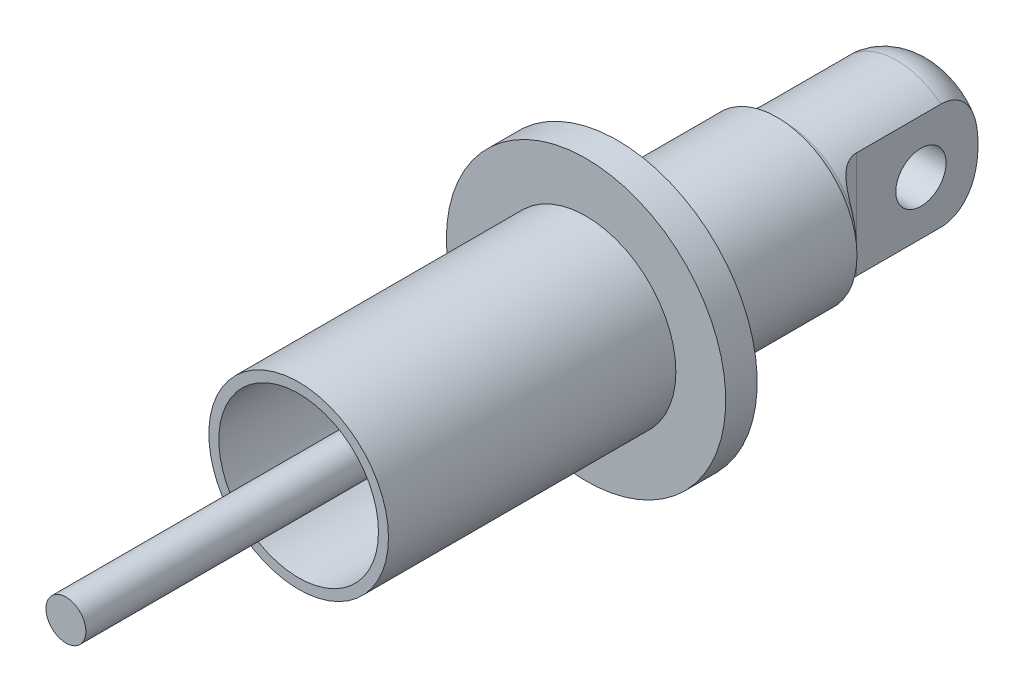
SolidWorks part; units mm, degrees
ref_plane "Front Plane" through (0, 0, 0) normal (0, 0, 1) x (1, 0, 0)
ref_plane "Top Plane" through (0, 0, 0) normal (0, 1, 0) x (1, 0, 0)
ref_plane "Right Plane" through (0, 0, 0) normal (1, 0, 0) x (0, 0, -1)
sketch "Sketch1" plane through (0, 0, 0) normal (0, 0, 1) x (1, 0, 0)
  circle A0 centre (0, 0) radius 12.7
extrude "Boss-Extrude1" add sketch "Sketch1" along normal blind 25.4
ref_plane "Plane1" through (0, 0, 0) normal (0, 1, 0) x (1, 0, 0)
sketch "Sketch3" plane through (0, 0, 0) normal (0, 1, 0) x (1, 0, 0)
  line L0 (12.7, 0) -> (-12.7, 0) construction
  line L2 (0, 0) -> (0, 25.4) construction
  line L3 (0, 25.4) -> (4.65, 25.4)
  line L4 (11, 19.05) -> (11, 1.5875)
  line L5 (12.5875, 0) -> (12.7, 0)
  line L6 (12.5875, 0) -> (0, 0)
  line L7 (0, 0) -> (0, 25.4)
  arc A0 (11, 19.05) -> (4.65, 25.4) centre (4.65, 19.05) ccw
  arc A1 (12.5875, 0) -> (11, 1.5875) centre (12.5875, 1.5875) cw
  point P4 (0, 0)
  point P14 (11, 0)
  dimension "D1" = 6.35
  dimension "D2" = 1.5875
revolve "Revolve1" add sketch "Sketch3" angle 360 about L2
ref_plane "Plane2" through (0, 11, 0) normal (0, 1, 0) x (1, 0, 0)
sketch "Sketch4" plane through (0, 11, 0) normal (0, 1, 0) x (1, 0, 0)
  line L0 (0, 1.5875) -> (0, 25.4) construction
  line L1 (11, 1.5875) -> (-11, 1.5875) construction
  line L2 (4.65, 25.4) -> (-4.65, 25.4) construction
  line L4 (-7, 1.5875) -> (7, 1.5875)
  line L5 (-7, 1.5875) -> (-7, 25.4)
  line L6 (-7, 25.4) -> (7, 25.4)
  line L7 (7, 1.5875) -> (7, 25.4)
  line L8 (-7, 1.5875) -> (7, 25.4) construction
  line L9 (-7, 25.4) -> (7, 1.5875) construction
  line L10 (-13.6862, 25.4) -> (13.6862, 25.4)
  line L11 (-13.6862, 25.4) -> (-13.6862, 1.5875)
  line L12 (-13.6862, 1.5875) -> (13.6862, 1.5875)
  line L13 (13.6862, 25.4) -> (13.6862, 1.5875)
  line L14 (-13.6862, 25.4) -> (13.6862, 1.5875) construction
  line L15 (-13.6862, 1.5875) -> (13.6862, 25.4) construction
  line L16 (-11, 5.5875) -> (11, 5.5875)
  circle A0 centre (-11, 5.5875) radius 4
  circle A1 centre (11, 5.5875) radius 4
  point P6 (0, 13.4938)
  point P11 (0, 13.4938)
extrude "Cut-Extrude1" cut sketch "Sketch4" against normal through all
sketch "Sketch6" plane through (7, 0, 0) normal (1, 0, 0) x (0, 0, -1)
  line L0 (0, 0) -> (15.875, 0) construction
  line L1 (0, -12.5875) -> (0, 12.5875) construction
  line L2 (55, 0) -> (-55, 0) construction
  circle A0 centre (15.875, 0) radius 4
extrude "Cut-Extrude2" cut sketch "Sketch6" against normal through all
sketch "Sketch7" plane through (0, 0, 0) normal (0, 1, 0) x (1, 0, 0)
  line L0 (14.2875, -25.4) -> (22.225, -25.4)
  line L2 (12.7, 0) -> (12.7, -23.8125)
  line L4 (22.225, -25.4) -> (22.225, -30.4)
  line L5 (22.225, -30.4) -> (0, -30.4)
  line L6 (0, -25.4) -> (0, -30.4) construction
  line L7 (12.7, -23.8125) -> (12.7, -25.4)
  line L8 (-12.7, -25.4) -> (12.7, -25.4) construction
  line L9 (12.7, -25.4) -> (0, -25.4)
  line L10 (12.7, -25.4) -> (12.7, -23.8125)
  arc A0 (12.7, -23.8125) -> (14.2875, -25.4) centre (14.2875, -23.8125) ccw
  dimension "D1" = 1.5875
revolve "Revolve2" add sketch "Sketch7" angle 360 about L6
sketch "Sketch8" plane through (0, 0, 30.4) normal (0, 0, 1) x (1, 0, 0)
  circle A0 centre (0, 0) radius 14.2875
  circle A1 centre (0, 0) radius 12.7
  dimension "D1" = 1.5875
extrude "Boss-Extrude2" add sketch "Sketch8" along normal blind 45.72
sketch "Sketch9" plane through (0, 0, 30.4) normal (0, 0, 1) x (1, 0, 0)
  circle A0 centre (0, 0) radius 3.175
extrude "Boss-Extrude3" add sketch "Sketch9" along normal blind 82.74
